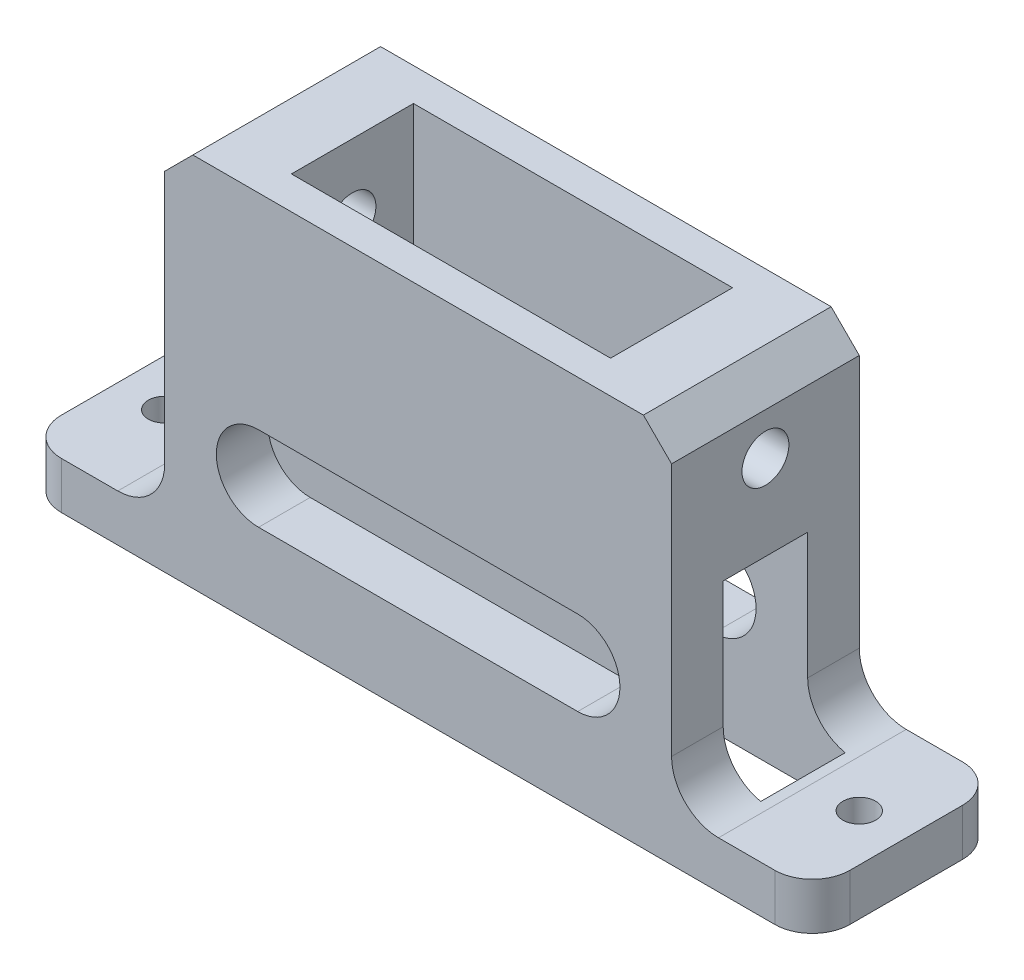
SolidWorks part; units mm, degrees
ref_plane "Front Plane" through (0, 0, 0) normal (0, 0, 1) x (1, 0, 0)
ref_plane "Top Plane" through (0, 0, 0) normal (0, 1, 0) x (1, 0, 0)
ref_plane "Right Plane" through (0, 0, 0) normal (1, 0, 0) x (0, 0, -1)
sketch "Sketch1" plane through (0, 0, 0) normal (0, 1, 0) x (1, 0, 0)
  line L1 (-27, 10) -> (27, 10)
  line L2 (-27, 10) -> (-27, -10)
  line L3 (-27, -10) -> (27, -10)
  line L4 (27, 10) -> (27, -10)
  line L5 (-27, 10) -> (27, -10) construction
  line L6 (-27, -10) -> (27, 10) construction
  point P0 (0, 0)
  dimension "D1" = 20
  dimension "D2" = 54
extrude "Boss-Extrude1" add sketch "Sketch1" along normal blind 40
sketch "Sketch4" plane through (0, 0, 0) normal (0, -1, 0) x (1, 0, 0)
  line L0 (27, -10) -> (-27, -10) construction
  line L1 (-27, 10) -> (-42, 10)
  line L2 (-27, 10) -> (-27, -10)
  line L3 (-27, -10) -> (-42, -10)
  line L4 (-42, 10) -> (-42, -10)
  line L5 (0, -11) -> (0, 11) construction
  line L6 (42, 10) -> (42, -10)
  line L7 (27, -10) -> (42, -10)
  line L8 (27, 10) -> (27, -10)
  line L9 (27, 10) -> (42, 10)
  dimension "D1" = 15
extrude "Boss-Extrude2" add sketch "Sketch4" against normal blind 5
fillet "Fillet1" radius 5 2 edges at (27, 5, 0) (-27, 5, 0)
sketch "Sketch6" plane through (0, 40, 0) normal (0, -1, 0) x (1, 0, 0)
  line L0 (17, 6.5) -> (-17, -6.5) construction
  line L1 (-17, 6.5) -> (17, 6.5)
  line L2 (-17, 6.5) -> (-17, -6.5)
  line L3 (-17, -6.5) -> (17, -6.5)
  line L4 (17, 6.5) -> (17, -6.5)
  line L5 (-27, -10) -> (-27, 10) construction
  dimension "D1" = 10
  dimension "D2" = 13
extrude "Cut-Extrude3" cut sketch "Sketch6" along normal offset from surface (26.35 mm away) 13.65 up to face at (0, 0, 0)
sketch "Sketch7" plane through (0, 0, 10) normal (0, 0, 1) x (1, 0, 0)
  line L0 (-17, 13.65) -> (17, 13.65) construction
  line L4 (-17, 18.15) -> (17, 18.15)
  line L8 (-17, 9.15) -> (17, 9.15)
  line L9 (0, 0) -> (0, 40) construction
  line L10 (-27, 40) -> (27, 40) construction
  line L11 (-17, 13.65) -> (-17, 40) construction
  line L12 (-42, 0) -> (42, 0) construction
  arc A2 (-17, 18.15) -> (-17, 9.15) centre (-17, 13.65) ccw
  arc A3 (17, 9.15) -> (17, 18.15) centre (17, 13.65) ccw
  point P2 (0, 13.65)
  dimension "D1" = 9
  dimension "D2" = 13.65
extrude "Cut-Extrude4" cut sketch "Sketch7" against normal through all
sketch "Sketch3" plane through (-27, 0, 0) normal (-1, 0, 0) x (0, 0, 1)
  line L2 (-10, 32.52) -> (10, 32.52) construction
  line L3 (-10, 40) -> (-10, 10) construction
  line L4 (10, 40) -> (10, 10) construction
  line L6 (10, 0) -> (-10, 0) construction
  line L7 (-10, 40) -> (-10, 10) construction
  line L8 (-10, 13.65) -> (-10, 32.52) construction
  circle A0 centre (0, 32.52) radius 2.5
  dimension "D1" = 5
  dimension "D2" = 13.65
  dimension "D3" = 18.87
extrude "Cut-Extrude2" cut sketch "Sketch3" against normal through all
ref_plane "Plane2" through (0, 0, -4.5) normal (0, 0, -1) x (-1, 0, 0)
sketch "Sketch8" plane through (0, 0, -4.5) normal (0, 0, -1) x (-1, 0, 0)
  line L0 (-17, 13.65) -> (17, 13.65) construction
  line L1 (-17, 27.65) -> (17, 27.65)
  line L3 (31, 13.65) -> (31, 0)
  line L4 (31, 0) -> (-31, 0)
  line L5 (-31, 0) -> (-31, 13.65)
  line L6 (42, 0) -> (-42, 0) construction
  arc A1 (-17, 27.65) -> (-31, 13.65) centre (-17, 13.65) ccw
  arc A3 (31, 13.65) -> (17, 27.65) centre (17, 13.65) ccw
  point P3 (0, 13.65)
  dimension "D1" = 14
extrude "Cut-Extrude5" cut sketch "Sketch8" against normal blind 9
sketch "Sketch9" plane through (0, 5, 0) normal (0, 1, 0) x (1, 0, 0)
  line L0 (-32, 0) -> (-42, 0) construction
  line L1 (-32, -10) -> (-32, 10) construction
  line L2 (-42, -10) -> (-42, 10) construction
  line L3 (32, 0) -> (42, 0) construction
  line L4 (32, 10) -> (32, -10) construction
  line L5 (42, 10) -> (42, -10) construction
  circle A0 centre (-37, 0) radius 1.75
  circle A1 centre (37, 0) radius 1.75
  dimension "D1" = 3.5
  dimension "D2" = 3.5
extrude "Cut-Extrude6" cut sketch "Sketch9" against normal through all
fillet "Fillet2" radius 4 4 edges at (-42, 2.5, -10) (42, 2.5, 10) (42, 2.5, -10) (-42, 2.5, 10)
chamfer "Chamfer1" distance 3 angle 45 2 edges at (27, 40, 0) (-27, 40, 0)
